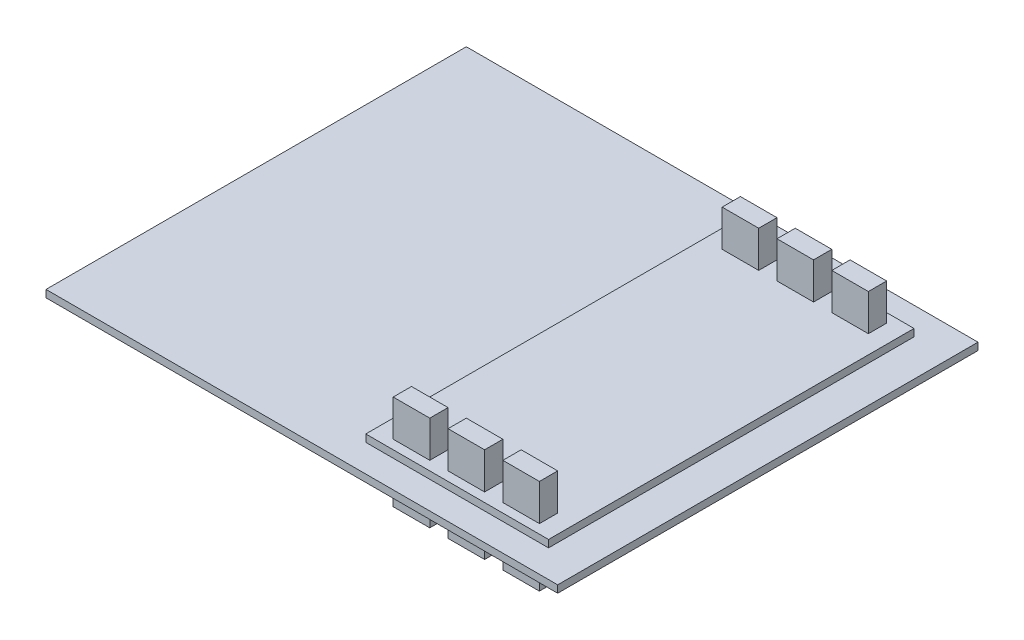
SolidWorks part; units mm, degrees
ref_plane "Front Plane" through (0, 0, 0) normal (0, 0, 1) x (1, 0, 0)
ref_plane "Top Plane" through (0, 0, 0) normal (0, 1, 0) x (1, 0, 0)
ref_plane "Right Plane" through (0, 0, 0) normal (1, 0, 0) x (0, 0, -1)
sketch "Sketch1" plane through (0, 0, 0) normal (0, 1, 0) x (1, 0, 0)
  line L1 (88.9, 73.025) -> (-88.9, 73.025)
  line L2 (88.9, 73.025) -> (88.9, -73.025)
  line L3 (88.9, -73.025) -> (-88.9, -73.025)
  line L4 (-88.9, 73.025) -> (-88.9, -73.025)
  line L5 (88.9, 73.025) -> (-88.9, -73.025) construction
  line L6 (88.9, -73.025) -> (-88.9, 73.025) construction
  point P0 (0, 0)
  dimension "D1" = 146.05
  dimension "D2" = 177.8
extrude "Boss-Extrude1" add sketch "Sketch1" along normal blind 2.54
sketch "Sketch2" plane through (0, 2.54, 0) normal (0, 1, 0) x (1, 0, 0)
  line L0 (88.9, 0) -> (0, 0) construction
  line L1 (88.9, -73.025) -> (88.9, 73.025) construction
  line L2 (44.45, 0) -> (44.45, 73.025) construction
  line L3 (88.9, 73.025) -> (-88.9, 73.025) construction
  line L4 (44.45, 73.025) -> (44.45, -73.025) construction
  line L5 (-88.9, -73.025) -> (88.9, -73.025) construction
  line L7 (76.2, 63.5) -> (12.7, 63.5)
  line L8 (76.2, 63.5) -> (76.2, -63.5)
  line L9 (76.2, -63.5) -> (12.7, -63.5)
  line L10 (12.7, 63.5) -> (12.7, -63.5)
  line L11 (76.2, 63.5) -> (12.7, -63.5) construction
  line L12 (76.2, -63.5) -> (12.7, 63.5) construction
  dimension "D1" = 63.5
  dimension "D2" = 127
extrude "Boss-Extrude2" add sketch "Sketch2" along normal blind 2.54 and the other way blind 5.08
sketch "Sketch3" plane through (0, 5.08, 0) normal (0, 1, 0) x (1, 0, 0)
  line L0 (12.7, 57.15) -> (76.2, 57.15) construction
  line L1 (12.7, 63.5) -> (12.7, -63.5) construction
  line L2 (76.2, -63.5) -> (76.2, 63.5) construction
  line L3 (12.7, 0) -> (76.2, 0) construction
  line L4 (19.05, 60.325) -> (31.75, 60.325)
  line L5 (19.05, 60.325) -> (19.05, 53.975)
  line L6 (19.05, 53.975) -> (31.75, 53.975)
  line L7 (31.75, 60.325) -> (31.75, 53.975)
  line L8 (19.05, 60.325) -> (31.75, 53.975) construction
  line L9 (19.05, 53.975) -> (31.75, 60.325) construction
  line L10 (38.1, 60.325) -> (50.8, 60.325)
  line L11 (38.1, 60.325) -> (38.1, 53.975)
  line L12 (38.1, 53.975) -> (50.8, 53.975)
  line L13 (50.8, 60.325) -> (50.8, 53.975)
  line L14 (38.1, 60.325) -> (50.8, 53.975) construction
  line L15 (38.1, 53.975) -> (50.8, 60.325) construction
  line L16 (57.15, 60.325) -> (69.85, 60.325)
  line L17 (57.15, 60.325) -> (57.15, 53.975)
  line L18 (57.15, 53.975) -> (69.85, 53.975)
  line L19 (69.85, 60.325) -> (69.85, 53.975)
  line L20 (57.15, 60.325) -> (69.85, 53.975) construction
  line L21 (57.15, 53.975) -> (69.85, 60.325) construction
  line L22 (57.15, -53.975) -> (69.85, -60.325) construction
  line L23 (57.15, -60.325) -> (69.85, -53.975) construction
  line L24 (38.1, -53.975) -> (50.8, -60.325) construction
  line L25 (38.1, -60.325) -> (50.8, -53.975) construction
  line L26 (19.05, -53.975) -> (31.75, -60.325) construction
  line L27 (19.05, -60.325) -> (31.75, -53.975) construction
  line L28 (12.7, -57.15) -> (76.2, -57.15) construction
  line L29 (69.85, -60.325) -> (69.85, -53.975)
  line L30 (57.15, -53.975) -> (69.85, -53.975)
  line L31 (57.15, -60.325) -> (57.15, -53.975)
  line L32 (57.15, -60.325) -> (69.85, -60.325)
  line L33 (50.8, -60.325) -> (50.8, -53.975)
  line L34 (38.1, -53.975) -> (50.8, -53.975)
  line L35 (38.1, -60.325) -> (38.1, -53.975)
  line L36 (38.1, -60.325) -> (50.8, -60.325)
  line L37 (31.75, -60.325) -> (31.75, -53.975)
  line L38 (19.05, -60.325) -> (19.05, -53.975)
  line L39 (19.05, -60.325) -> (31.75, -60.325)
  line L40 (19.05, -53.975) -> (31.75, -53.975)
  point P6 (25.4, 57.15)
  point P11 (44.45, 57.15)
  point P16 (63.5, 57.15)
  point P38 (63.5, -57.15)
  point P39 (44.45, -57.15)
  point P40 (25.4, -57.15)
  dimension "D1" = 6.35
  dimension "D2" = 3.175
  dimension "D3" = 12.7
  dimension "D4" = 31.75
  dimension "D5" = 19.05
  dimension "D6" = 19.05
extrude "Boss-Extrude3" add sketch "Sketch3" along normal blind 12.7 and the other way blind 20.32
